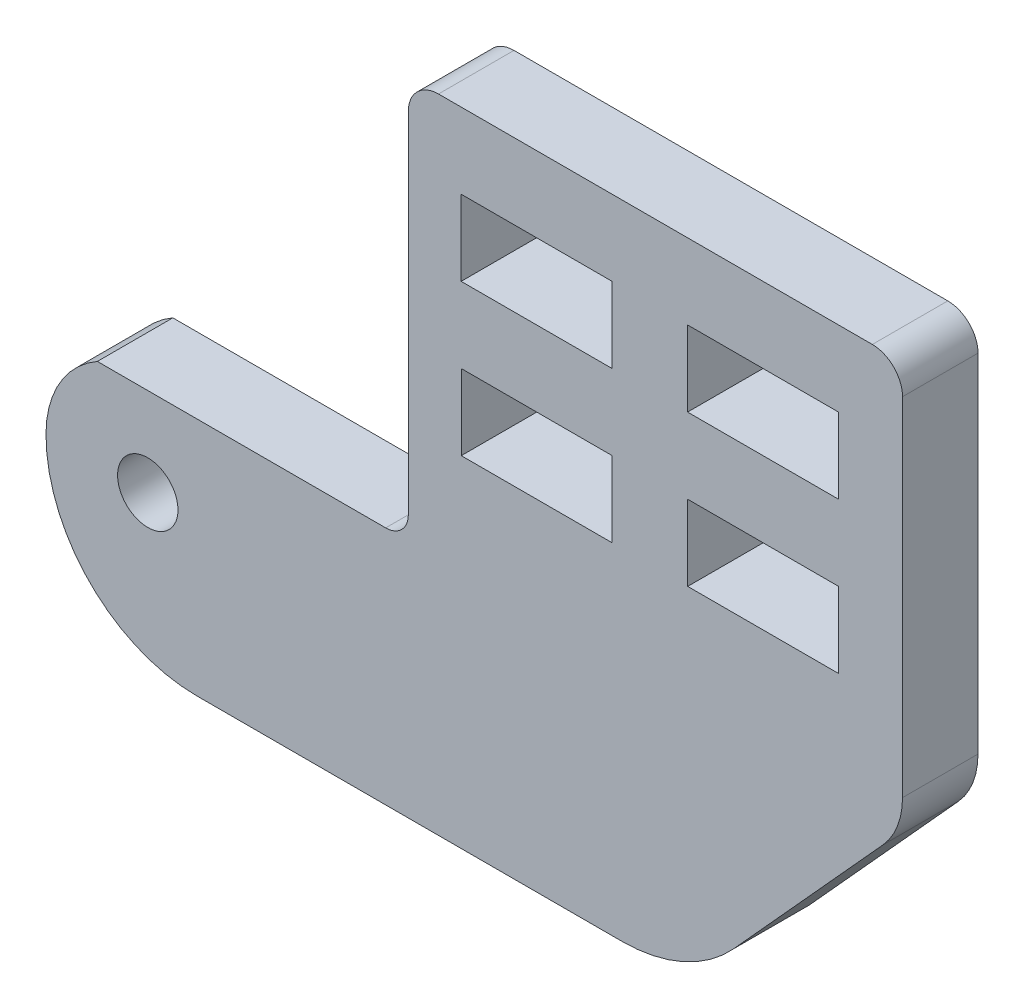
SolidWorks part; units mm, degrees
ref_plane "Front Plane" through (0, 0, 0) normal (0, 0, 1) x (1, 0, 0)
ref_plane "Top Plane" through (0, 0, 0) normal (0, 1, 0) x (1, 0, 0)
ref_plane "Right Plane" through (0, 0, 0) normal (1, 0, 0) x (0, 0, -1)
sketch "Sketch1" plane through (0, 0, 0) normal (0, 0, 1) x (1, 0, 0)
  line L0 (-1.742, -10.0393) -> (26.4116, -10.0393)
  line L1 (45, 7.5) -> (45, 30.5)
  line L2 (10.7604, 5.8562) -> (-8.3404, 5.8562)
  line L3 (43.7036, 4.1409) -> (33.8187, -6.7575)
  line L4 (15.7604, 27.5) -> (25.7604, 27.5)
  line L5 (14.2604, 32.5) -> (43, 32.5)
  line L6 (12.2604, 7.3562) -> (12.2604, 30.5)
  line L7 (15.7604, 27.5) -> (15.7604, 22.5)
  line L8 (15.7604, 22.5) -> (25.7604, 22.5)
  line L9 (25.7604, 27.5) -> (25.7604, 22.5)
  line L10 (30.7604, 27.5) -> (40.7604, 27.5)
  line L11 (30.7604, 27.5) -> (30.7604, 22.5)
  line L12 (30.7604, 22.5) -> (40.7604, 22.5)
  line L13 (40.7604, 27.5) -> (40.7604, 22.5)
  line L15 (15.7686, 17.5031) -> (25.7686, 17.5031)
  line L16 (15.7686, 17.5031) -> (15.7686, 12.5031)
  line L17 (15.7686, 12.5031) -> (25.7686, 12.5031)
  line L18 (25.7686, 17.5031) -> (25.7686, 12.5031)
  line L19 (30.7686, 17.5031) -> (40.7686, 17.5031)
  line L20 (30.7686, 17.5031) -> (30.7686, 12.5031)
  line L21 (30.7686, 12.5031) -> (40.7686, 12.5031)
  line L22 (40.7686, 17.5031) -> (40.7686, 12.5031)
  circle A0 centre (-5, 0) radius 2
  arc A1 (-11.7419, 0) -> (-8.3404, 5.8562) centre (-5, 0) cw
  arc A2 (12.2604, 7.3562) -> (10.7604, 5.8562) centre (10.7604, 7.3562) cw
  arc A3 (45, 30.5) -> (43, 32.5) centre (43, 30.5) ccw
  arc A4 (12.2604, 30.5) -> (14.2604, 32.5) centre (14.2604, 30.5) cw
  arc A5 (33.8187, -6.7575) -> (26.4116, -10.0393) centre (26.4116, -0.0393) cw
  arc A6 (45, 7.5) -> (43.7036, 4.1409) centre (40, 7.5) cw
  arc A7 (-11.7419, 0) -> (-1.742, -10.0393) centre (-1.742, -0.0393) ccw
  dimension "D2" = 1.5
  dimension "D3" = 2
  dimension "D4" = 2
  dimension "D9" = 10
  dimension "D12" = 5
  dimension "D13" = 5
  dimension "D5" = 10
  dimension "D6" = 10
  dimension "D7" = 5
  dimension "D8" = 5
  dimension "D10" = 5
  dimension "D11" = 5
extrude "Boss-Extrude1" add sketch "Sketch1" along normal blind 5
